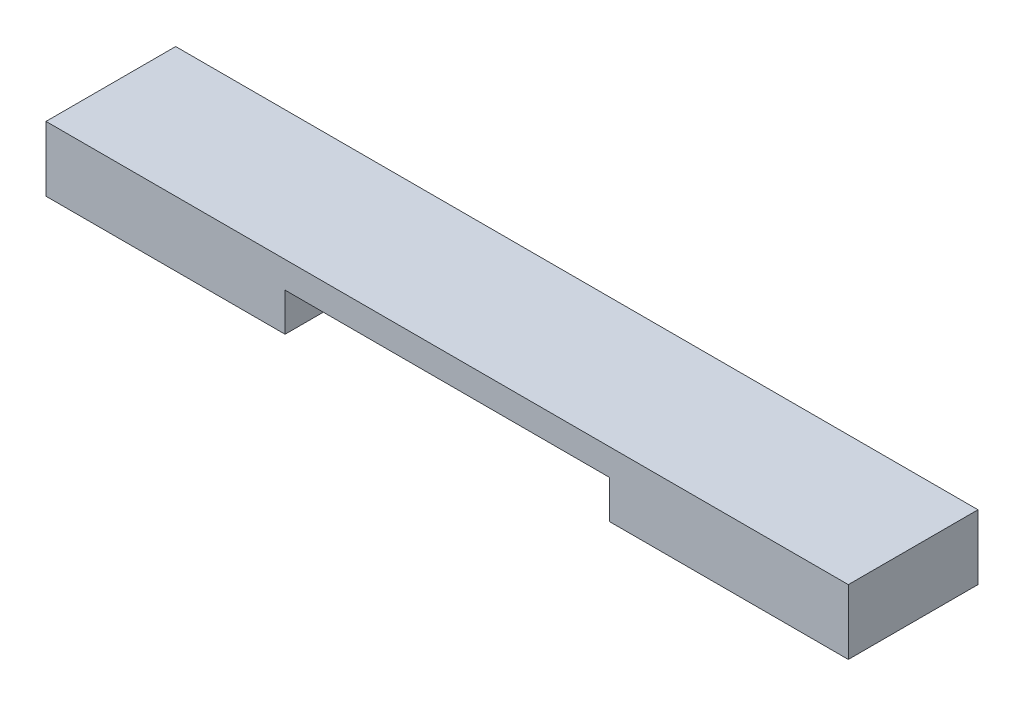
SolidWorks part; units mm, degrees
ref_plane "Front Plane" through (0, 0, 0) normal (0, 0, 1) x (1, 0, 0)
ref_plane "Top Plane" through (0, 0, 0) normal (0, 1, 0) x (1, 0, 0)
ref_plane "Right Plane" through (0, 0, 0) normal (1, 0, 0) x (0, 0, -1)
sketch "Sketch1" plane through (0, 0, 0) normal (0, 0, 1) x (1, 0, 0)
  line L0 (-10, -0.82) -> (-24.75, -0.82) construction
  line L1 (-24.75, -2) -> (-10, -2)
  line L2 (-24.75, -2) -> (-24.75, 2)
  line L3 (-24.75, 2) -> (24.75, 2)
  line L4 (24.75, -2) -> (24.75, 2)
  line L5 (0, 2) -> (0, 0) construction
  line L6 (-24.75, 0) -> (0, 0) construction
  line L8 (-10, -2) -> (-10, 0.36)
  line L9 (-10, 0.36) -> (10, 0.36)
  line L10 (10, -2) -> (10, 0.36)
  line L11 (10, -0.82) -> (24.75, -0.82) construction
  line L12 (10, -2) -> (24.75, -2)
  point P0 (0, 0)
  dimension "D1" = 49.5
  dimension "D2" = 4
  dimension "D3" = 2.36
  dimension "D4" = 20
extrude "Boss-Extrude1" add sketch "Sketch1" along normal blind 8
